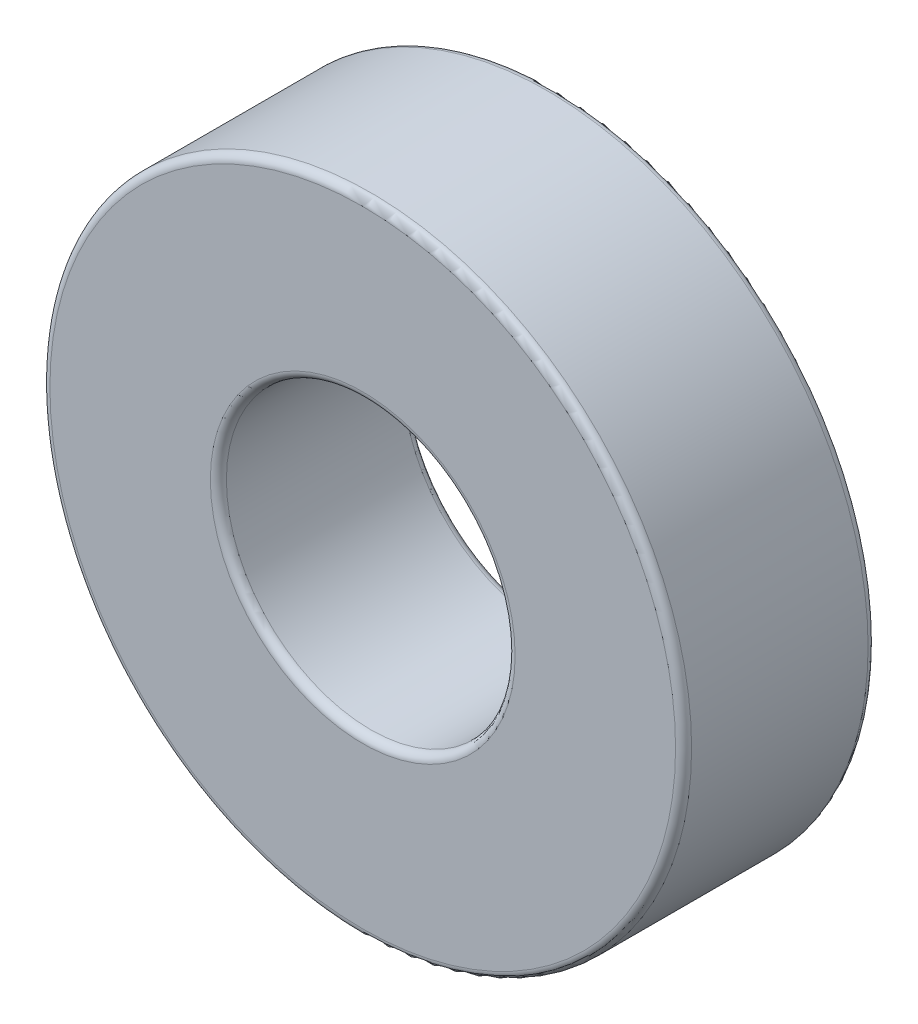
SolidWorks part; units mm, degrees
ref_plane "Płaszczyzna przednia" through (0, 0, 0) normal (0, 0, 1) x (1, 0, 0)
ref_plane "Płaszczyzna górna" through (0, 0, 0) normal (0, 1, 0) x (1, 0, 0)
ref_plane "Płaszczyzna prawa" through (0, 0, 0) normal (1, 0, 0) x (0, 0, -1)
sketch "Szkic1" plane through (0, 0, 0) normal (0, 0, 1) x (1, 0, 0)
  circle A0 centre (0, 0) radius 20
  dimension "D1" = 40
extrude "Dodanie-wyciągnięcie1" add sketch "Szkic1" along normal blind 12
sketch "Szkic4" plane through (0, 0, 0) normal (0, 0, -1) x (-1, 0, 0)
  circle A0 centre (0, 0) radius 9
  dimension "D1" = 18
extrude "Wytnij-wyciągnięcie1" cut sketch "Szkic4" against normal blind 12
fillet "Zaokrąglenie1" radius 0.5 4 edges at (20, 0, 0) (20, 0, 12) (-9, 0, 12) (-9, 0, 0)
